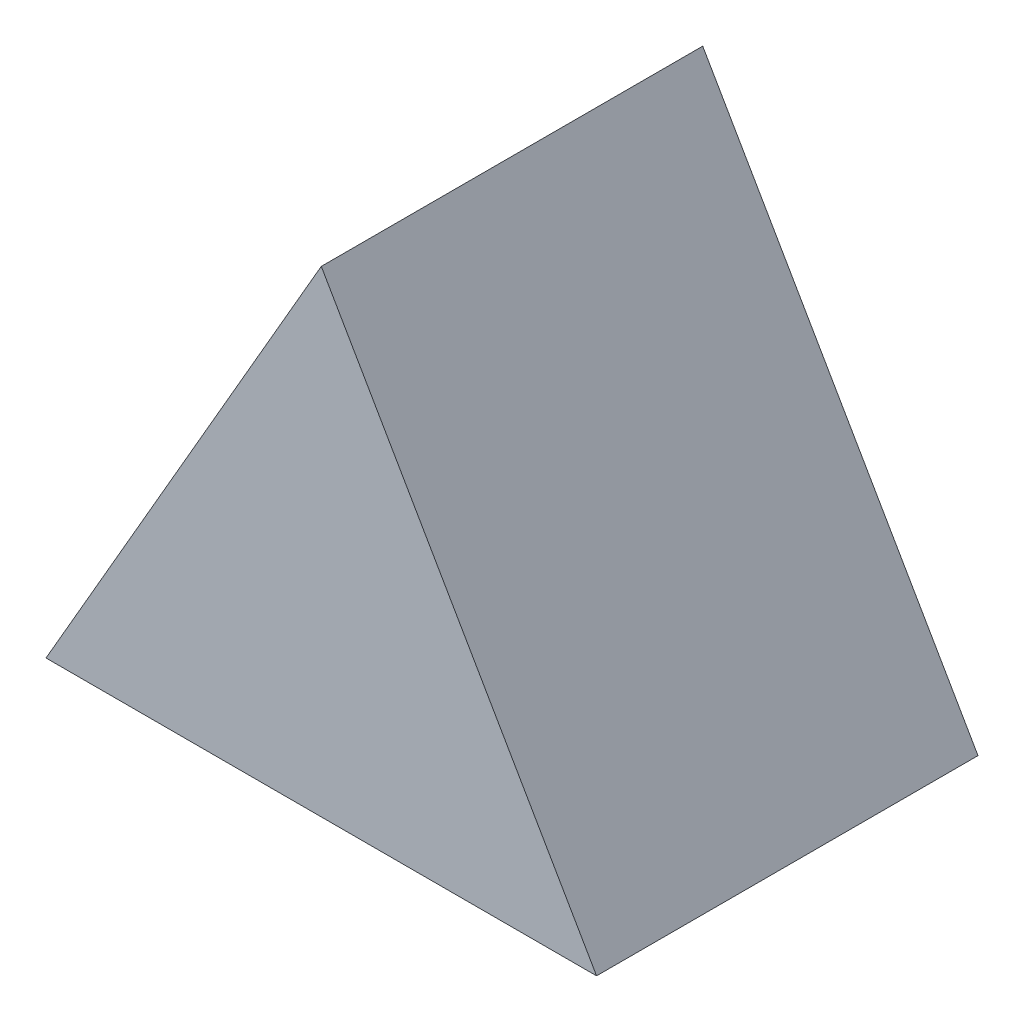
SolidWorks part; units mm, degrees
ref_plane "Piano frontale" through (0, 0, 0) normal (0, 0, 1) x (1, 0, 0)
ref_plane "Piano superiore" through (0, 0, 0) normal (0, 1, 0) x (1, 0, 0)
ref_plane "Piano destro" through (0, 0, 0) normal (1, 0, 0) x (0, 0, -1)
sketch "Schizzo1" plane through (0, 0, 0) normal (0, 0, 1) x (1, 0, 0)
  line L1 (0, 25) -> (-21.6506, -12.5)
  line L2 (-21.6506, -12.5) -> (21.6506, -12.5)
  line L3 (21.6506, -12.5) -> (0, 25)
  circle A0 centre (0, 0) radius 25 construction
  dimension "D1" = 50
extrude "Estrusione-Estrusione1" add sketch "Schizzo1" along normal blind 30
